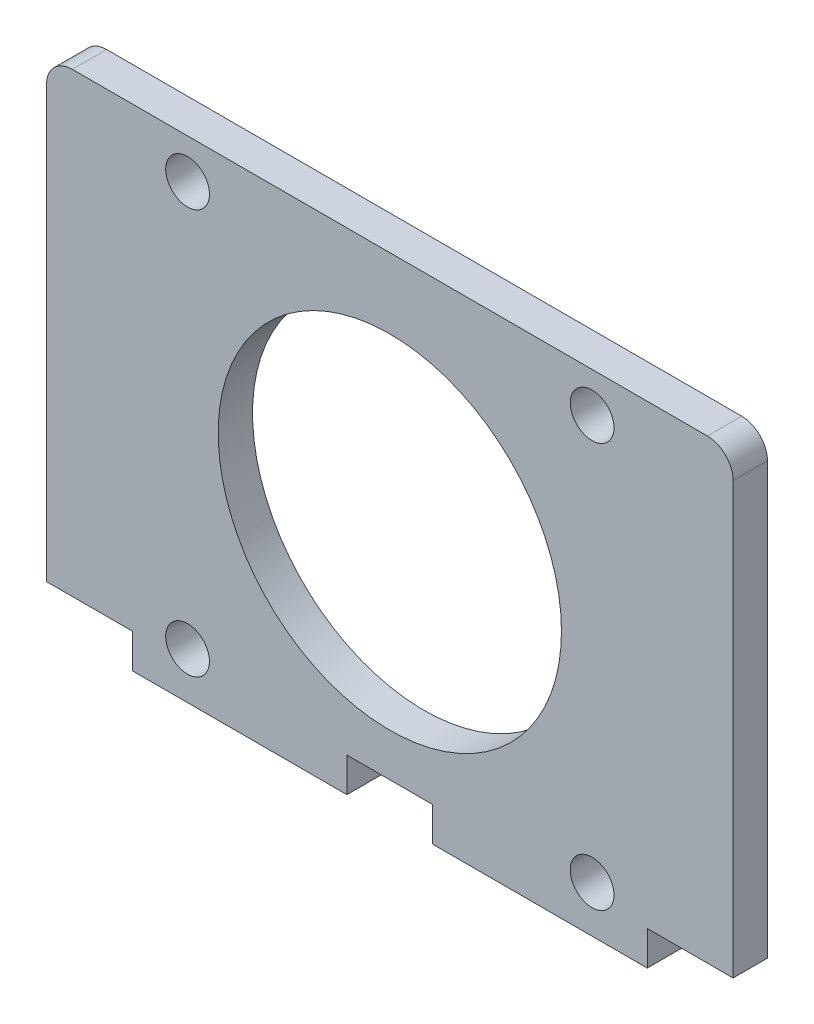
SolidWorks part; units mm, degrees
ref_plane "Спереди" through (0, 0, 0) normal (0, 0, 1) x (1, 0, 0)
ref_plane "Сверху" through (0, 0, 0) normal (0, 1, 0) x (1, 0, 0)
ref_plane "Справа" through (0, 0, 0) normal (1, 0, 0) x (0, 0, -1)
sketch "Эскиз1" plane through (0, 0, 0) normal (0, 0, 1) x (1, 0, 0)
  line L0 (-40, 0) -> (40, 0)
  line L1 (-40, 0) -> (-40, -53.2)
  line L2 (-40, -53.2) -> (-30, -53.2)
  line L3 (-30, -53.2) -> (-30, -57.2)
  line L4 (-30, -57.2) -> (-5, -57.2)
  line L5 (30, -57.2) -> (30, -53.2)
  line L6 (30, -53.2) -> (40, -53.2)
  line L7 (-5, -57.2) -> (-5, -53.2)
  line L8 (-5, -53.2) -> (5, -53.2)
  line L9 (5, -53.2) -> (5, -57.2)
  line L10 (5, -57.2) -> (30, -57.2)
  line L11 (40, -53.2) -> (40, 0)
  line L12 (-23.57, -4.63) -> (0, -28.2) construction
  line L13 (0, -28.2) -> (0, -4.63) construction
  line L14 (0, -4.63) -> (-23.57, -4.63) construction
  circle A0 centre (0, -28.2) radius 20
  circle A1 centre (-23.57, -4.63) radius 2.55
  circle A2 centre (23.57, -4.63) radius 2.55
  circle A3 centre (23.57, -51.77) radius 2.55
  circle A4 centre (-23.57, -51.77) radius 2.55
  point P0 (5, -59.9455)
  point P4 (0, 0)
  point P27 (0, -28.2)
  dimension "D2" = 40
  dimension "D4" = 45
  dimension "D6" = 28.2
  dimension "D5" = 47.14
  dimension "D7" = 5.1
  dimension "D1" = 53.2
  dimension "D8" = 80
  dimension "D9" = 4
  dimension "D10" = 10
  dimension "D3" = 4
extrude "Бобышка-Вытянуть2" add sketch "Эскиз1" along normal blind 4
fillet "Скругление1" radius 3 2 edges at (-40, 0, 2) (40, 0, 2)
